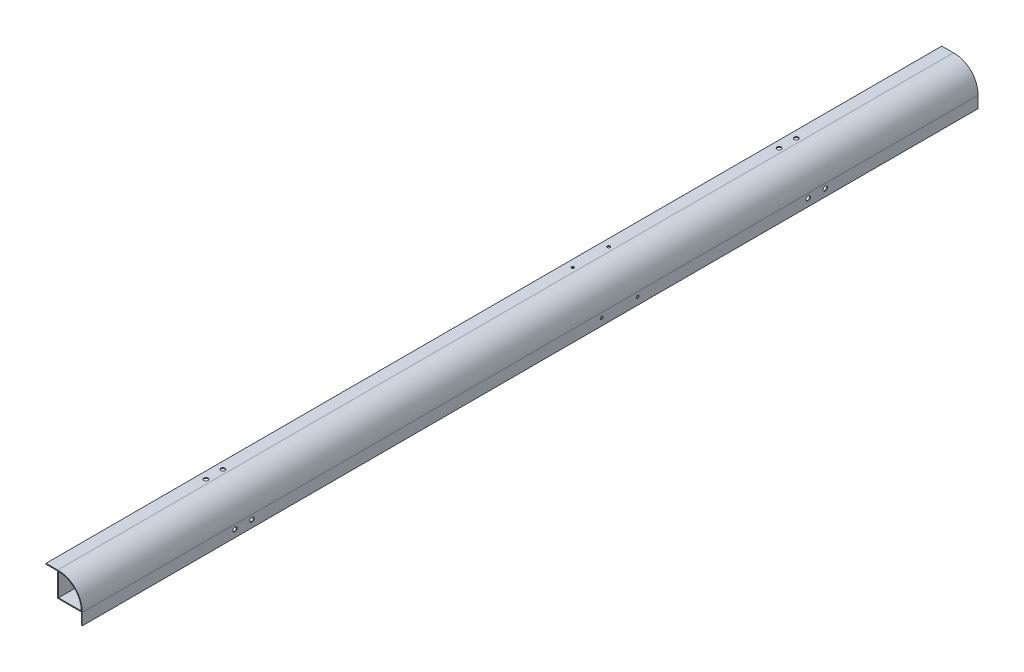
SolidWorks part; units mm, degrees
ref_plane "Alzado" through (0, 0, 0) normal (0, 0, 1) x (1, 0, 0)
ref_plane "Planta" through (0, 0, 0) normal (0, 1, 0) x (1, 0, 0)
ref_plane "Vista lateral" through (0, 0, 0) normal (1, 0, 0) x (0, 0, -1)
sketch "Croquis1" plane through (0, 0, 0) normal (0, 0, 1) x (1, 0, 0)
  line L0 (-13.7, -13.7) -> (13.6811, -13.7)
  line L1 (-12.7, -12.7) -> (12.7, -12.7)
  line L2 (-12.7, -12.7) -> (-12.7, 12.7)
  line L5 (0, 16.5842) -> (0, -23.118) construction
  line L6 (-13.7, -13.7) -> (-13.7, 13.6811)
  line L8 (-18.0998, 0) -> (17.5647, 0) construction
  line L9 (13.6811, -13.7) -> (12.6811, -13.7)
  line L10 (13.6811, -13.7) -> (13.6811, -26.7)
  line L11 (13.6811, -26.7) -> (12.6811, -26.7)
  line L12 (12.6811, -13.7) -> (12.6811, -26.7)
  line L13 (-13.7, 13.6811) -> (-26.7, 13.6811)
  line L14 (-13.7, 13.6811) -> (-13.7, 12.6811)
  line L15 (-13.7, 12.6811) -> (-26.7, 12.6811)
  line L16 (-26.7, 13.6811) -> (-26.7, 12.6811)
  arc A0 (-12.7, 12.7) -> (12.7, -12.7) centre (-12.7, -12.7) cw
  arc A1 (-13.7, 13.6811) -> (13.6811, -13.7) centre (-12.7, -12.7) cw
  point P0 (0, 0)
  point P12 (-12.7, 0)
  point P13 (0, -12.7)
  dimension "D3" = 25.4
  dimension "D1" = 25.4
  dimension "D2" = 25.4
  dimension "D5" = 1
  dimension "D6" = 13
  dimension "D7" = 1
  dimension "D8" = 13
  dimension "D4" = 1
extrude "Saliente-Extruir1" add sketch "Croquis1" along normal mid plane 1000 contours A1 L6 L0 L2 A0 L1 | L13 L16 L15 L6 | L0 L12 L11 L10
ref_plane "Plano1" through (-12.7, -12.7, 500) normal (0, 1, 0) x (1, 0, 0)
sketch "Croquis2" plane through (13.6811, 0, 0) normal (1, 0, 0) x (0, 0, -1)
  line L0 (0, 93.7538) -> (0, -74.3435) construction
  line L1 (560.0844, 0) -> (-573.6748, 0) construction
  line L2 (320, 46.1161) -> (320, -56.1874) construction
  line L3 (100, 46.1161) -> (100, -56.1874) construction
  line L4 (-500, -26.7) -> (500, -26.7) construction
  line L5 (-320, 46.1161) -> (-320, -56.1874) construction
  line L6 (-500, -13.7) -> (500, -13.7) construction
  circle A0 centre (310.5, -18.7) radius 2.3813
  circle A1 centre (329.5, -18.7) radius 2.3813
  circle A2 centre (310.5, -18.7) radius 2.3813
  circle A3 centre (329.5, -18.7) radius 2.3813
  circle A4 centre (310.5, -18.7) radius 2.3813
  circle A5 centre (329.5, -18.7) radius 2.3813
  circle A6 centre (310.5, -18.7) radius 2.3813
  circle A7 centre (329.5, -18.7) radius 2.3813
  circle A8 centre (-329.5, -18.7) radius 2.3813
  circle A9 centre (-310.5, -18.7) radius 2.3813
  circle A10 centre (-329.5, -18.7) radius 2.3813
  circle A11 centre (-310.5, -18.7) radius 2.3813
  circle A12 centre (-329.5, -18.7) radius 2.3813
  circle A13 centre (-310.5, -18.7) radius 2.3813
  circle A14 centre (-329.5, -18.7) radius 2.3813
  circle A15 centre (-310.5, -18.7) radius 2.3813
  circle A16 centre (120, -18.7) radius 1.5
  circle A17 centre (80, -18.7) radius 1.5
  dimension "D2" = 4.7625
  dimension "D7" = 3
  dimension "D1" = 9.5
  dimension "D3" = 320
  dimension "D4" = 8
  dimension "D5" = 100
  dimension "D6" = 20
  dimension "D8" = 5
extrude "Cortar-Extruir1" cut sketch "Croquis2" against normal blind 10 contours A1 | A0 | A15 | A14 | A17 | A16
sketch "Croquis3" plane through (0, 13.6811, 0) normal (0, 1, 0) x (1, 0, 0)
  line L0 (-69.3307, 320) -> (48.8112, 320) construction
  line L1 (-26.7, -500) -> (-26.7, 500) construction
  line L2 (-105.8003, 100) -> (67.0517, 100) construction
  line L3 (331.1987, 0) -> (-269.3715, 0) construction
  line L4 (-13.7, -500) -> (-13.7, 500) construction
  circle A0 centre (-18.7, 329.5) radius 2.3813
  circle A1 centre (-18.7, 310.5) radius 2.3813
  circle A2 centre (-18.7, -310.5) radius 2.3813
  circle A3 centre (-18.7, -329.5) radius 2.3813
  circle A4 centre (-18.7, 120) radius 1.5
  circle A5 centre (-18.7, 80) radius 1.5
  dimension "D1" = 4.7625
  dimension "D7" = 3
  dimension "D2" = 9.5
  dimension "D3" = 8
  dimension "D4" = 320
  dimension "D5" = 100
  dimension "D6" = 20
  dimension "D8" = 5
extrude "Cortar-Extruir2" cut sketch "Croquis3" against normal blind 10
